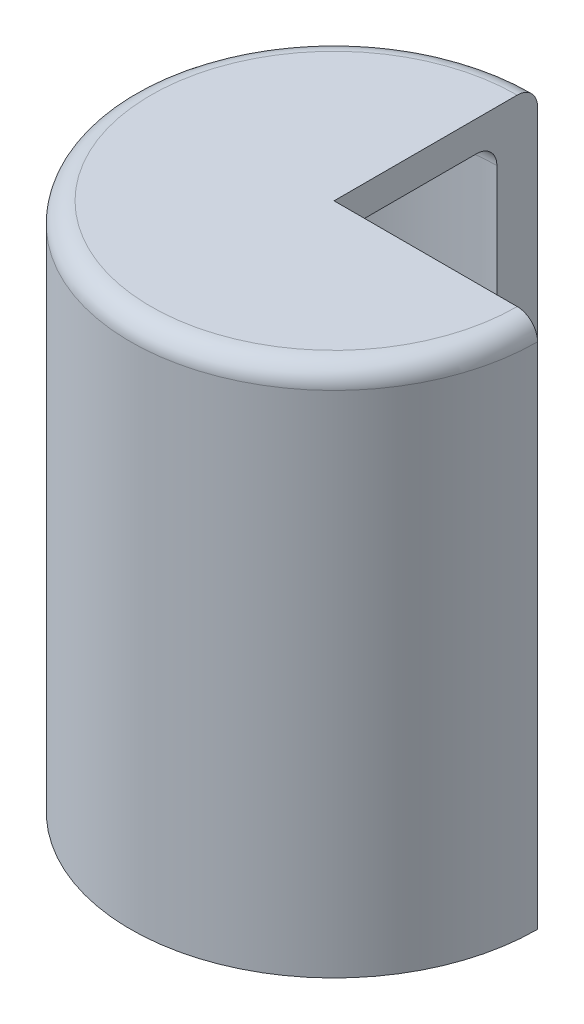
SolidWorks part; units mm, degrees
ref_plane "Front Plane" through (0, 0, 0) normal (0, 0, 1) x (1, 0, 0)
ref_plane "Top Plane" through (0, 0, 0) normal (0, 1, 0) x (1, 0, 0)
ref_plane "Right Plane" through (0, 0, 0) normal (1, 0, 0) x (0, 0, -1)
sketch "Sketch1" plane through (0, 0, 0) normal (0, 0, 1) x (1, 0, 0)
  line L0 (0, 40.2884) -> (0, -204.7423) construction
  line L1 (0, 40.2884) -> (70, 40.2884)
  line L2 (80, 30.2884) -> (80, -204.7423)
  line L3 (0, 40.2884) -> (0, 55.2577)
  line L4 (0, 55.2577) -> (90, 55.2577)
  line L5 (100, -204.7423) -> (100, 45.2577)
  line L6 (80, -204.7423) -> (100, -204.7423)
  arc A0 (100, 45.2577) -> (90, 55.2577) centre (90, 45.2577) ccw
  arc A1 (80, 30.2884) -> (70, 40.2884) centre (70, 30.2884) ccw
  point P14 (0, -82.2269)
  dimension "D2" = 10
  dimension "D1" = 20
  dimension "D3" = 80
  dimension "D4" = 250
revolve "Revolve1" add sketch "Sketch1" angle 270 about L0
